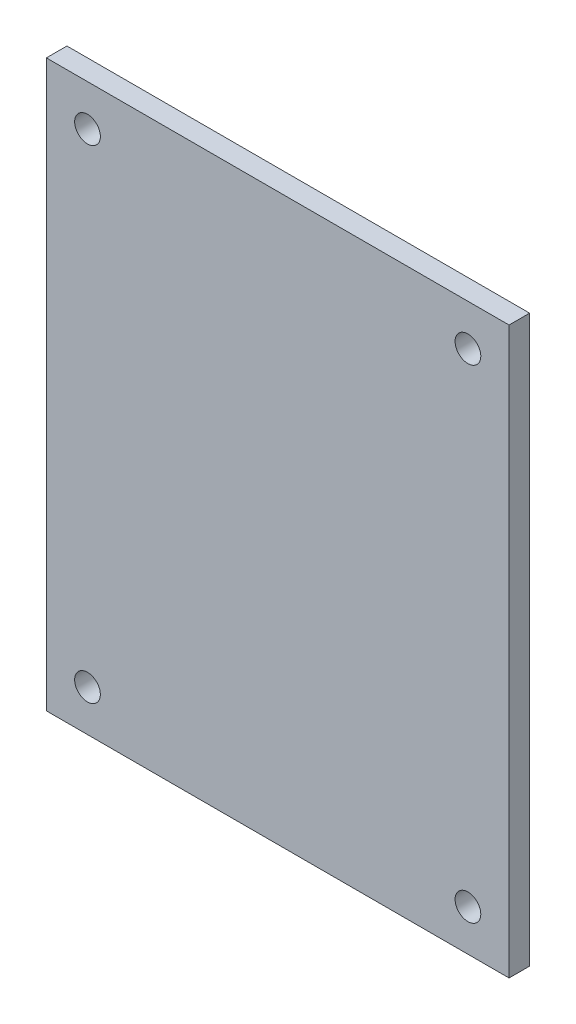
SolidWorks part; units mm, degrees
ref_plane "Alzado" through (0, 0, 0) normal (0, 0, 1) x (1, 0, 0)
ref_plane "Planta" through (0, 0, 0) normal (0, 1, 0) x (1, 0, 0)
ref_plane "Vista lateral" through (0, 0, 0) normal (1, 0, 0) x (0, 0, -1)
sketch "Croquis1" plane through (0, 0, 0) normal (0, 0, 1) x (1, 0, 0)
  line L0 (0, 0) -> (9.2614, 0) construction
  line L1 (-22.5, -27.5) -> (22.5, -27.5)
  line L2 (-22.5, -27.5) -> (-22.5, 27.5)
  line L3 (-22.5, 27.5) -> (22.5, 27.5)
  line L4 (22.5, -27.5) -> (22.5, 27.5)
  line L5 (-22.5, -27.5) -> (22.5, 27.5) construction
  line L6 (-22.5, 27.5) -> (22.5, -27.5) construction
  line L7 (0, 0) -> (0, 9.0643) construction
  line L8 (-22.5, 27.5) -> (-22.5, 23.5) construction
  line L9 (-22.5, 23.5) -> (-18.5, 23.5) construction
  circle A0 centre (-18.5, 23.5) radius 1.25
  circle A1 centre (18.5, 23.5) radius 1.25
  circle A2 centre (18.5, -23.5) radius 1.25
  circle A3 centre (-18.5, -23.5) radius 1.25
  point P0 (0, 0)
extrude "Saliente-Extruir1" add sketch "Croquis1" along normal blind 2
